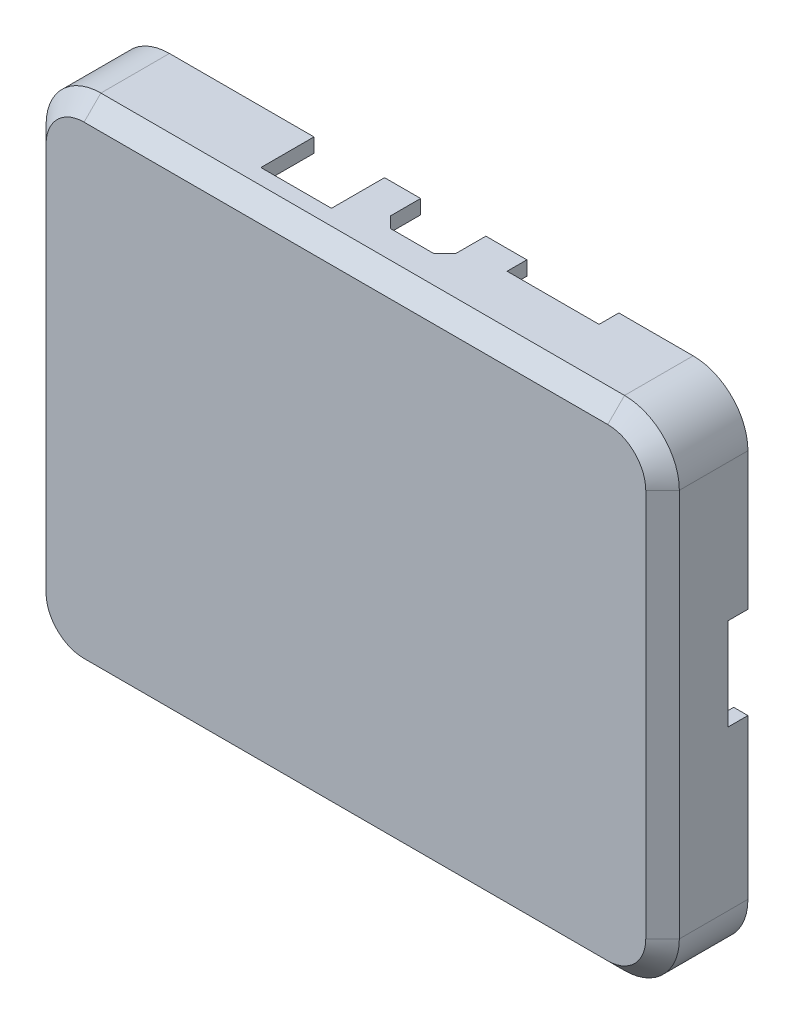
SolidWorks part; units mm, degrees
ref_plane "前基準面" through (0, 0, 0) normal (0, 0, 1) x (1, 0, 0)
ref_plane "上基準面" through (0, 0, 0) normal (0, 1, 0) x (1, 0, 0)
ref_plane "右基準面" through (0, 0, 0) normal (1, 0, 0) x (0, 0, -1)
sketch "草圖1" plane through (0, 0, 0) normal (0, 0, 1) x (1, 0, 0)
  line L1 (-44.5, 35) -> (44.5, 35)
  line L2 (-44.5, 35) -> (-44.5, -35)
  line L3 (-44.5, -35) -> (44.5, -35)
  line L4 (44.5, 35) -> (44.5, -35)
  line L5 (-44.5, 35) -> (44.5, -35) construction
  line L6 (-44.5, -35) -> (44.5, 35) construction
  point P0 (0, 0)
  dimension "D1" = 89
  dimension "D2" = 70
extrude "填料-伸長1" add sketch "草圖1" along normal blind 12
fillet "圓角1" radius 7.7 4 edges at (44.5, -35, 6) (44.5, 35, 6) (-44.5, -35, 6) (-44.5, 35, 6)
chamfer "導角1" distance 2.36 angle 45 8 edges at (-42.2447, -32.7447, 12) (-44.5, 0, 12) (-42.2447, 32.7447, 12) (0, 35, 12) (42.2447, 32.7447, 12) (44.5, 0, 12) (42.2447, -32.7447, 12) (0, -35, 12)
shell "薄殼1" thickness 2
sketch "草圖2" plane through (0, 35, 0) normal (0, 1, 0) x (1, 0, 0)
  line L0 (36.8, 0) -> (-36.8, 0) construction
  line L1 (-16.49, 0) -> (-6.57, 0)
  line L2 (-16.49, 0) -> (-16.49, -7.46)
  line L3 (-16.49, -7.46) -> (-6.57, -7.46)
  line L4 (-6.57, 0) -> (-6.57, -7.46)
  line L5 (-1.5, 0) -> (-1.5, -4.23)
  line L10 (13.43, 0) -> (26.36, 0)
  line L11 (13.43, 0) -> (13.43, -2.78)
  line L12 (13.43, -2.78) -> (26.36, -2.78)
  line L13 (26.36, 0) -> (26.36, -2.78)
  line L14 (-1.5, -4.23) -> (0.05, -5.7771)
  line L15 (0.05, -5.7771) -> (6.12, -5.7771)
  line L16 (6.12, -5.7771) -> (7.67, -4.23)
  line L17 (7.67, -4.23) -> (7.67, 0)
  line L18 (7.67, 0) -> (-1.5, 0)
  line L19 (-44.5, -9.64) -> (-44.5, 0) construction
  point P16 (3.085, -5.7771)
  point P17 (3.085, 0)
  dimension "D1" = 9.92
  dimension "D2" = 7.46
  dimension "D3" = 9.17
  dimension "D4" = 4.23
  dimension "D5" = 6.07
  dimension "D6" = 2.19
  dimension "D7" = 12.93
  dimension "D8" = 2.78
  dimension "D9" = 28.01
  dimension "D10" = 5.07
  dimension "D11" = 5.76
extrude "除料-伸長1" cut sketch "草圖2" against normal up to next
sketch "草圖3" plane through (-44.5, 0, 0) normal (-1, 0, 0) x (0, 0, 1)
  line L0 (0, 27.3) -> (0, -27.3) construction
  line L1 (0, 9.43) -> (2.78, 9.43)
  line L2 (0, 9.43) -> (0, -3.5)
  line L3 (0, -3.5) -> (2.78, -3.5)
  line L4 (2.78, 9.43) -> (2.78, -3.5)
  line L5 (9.64, -35) -> (0, -35) construction
  line L6 (0, -6.5) -> (6.7, -6.5)
  line L7 (0, -6.5) -> (0, -23.5)
  line L8 (0, -23.5) -> (6.7, -23.5)
  line L9 (6.7, -6.5) -> (6.7, -23.5)
  point P10 (1.39, -3.5)
  point P13 (4.82, -35)
  dimension "D1" = 12.93
  dimension "D2" = 2.78
  dimension "D3" = 17
  dimension "D4" = 6.7
  dimension "D5" = 3
  dimension "D6" = 11.5
extrude "除料-伸長2" cut sketch "草圖3" against normal up to next and the other way through all
sketch "草圖4" plane through (44.5, 0, 0) normal (1, 0, 0) x (0, 0, -1)
  line L0 (0, -27.3) -> (0, 27.3) construction
  line L1 (0, 8) -> (-2.78, 8)
  line L2 (0, 8) -> (0, -4.93)
  line L3 (0, -4.93) -> (-2.78, -4.93)
  line L4 (-2.78, 8) -> (-2.78, -4.93)
  line L6 (-9.64, 35) -> (0, 35) construction
  dimension "D1" = 12.93
  dimension "D2" = 2.78
  dimension "D3" = 27
extrude "除料-伸長3" cut sketch "草圖4" against normal up to next
sketch "草圖5" plane through (0, 0, 10) normal (0, 0, -1) x (-1, 0, 0)
  line L0 (-36.8, 31.8116) -> (36.8, 31.8116) construction
  line L1 (-41.3116, -27.3) -> (-41.3116, 27.3) construction
  line L2 (36.8, -31.8116) -> (-36.8, -31.8116) construction
  line L3 (41.3116, 27.3) -> (41.3116, -27.3) construction
  circle A0 centre (-35.3116, 25.8116) radius 4.5
  circle A1 centre (35.3116, 25.8116) radius 4.5
  circle A2 centre (35.3116, -25.8116) radius 4.5
  circle A3 centre (-35.3116, -25.8116) radius 4.5
  point P10 (0, 0)
  point P12 (-22.2328, 16.8849)
  point P14 (0, 0)
  point P15 (0, 0)
  point P16 (0, 0)
  point P17 (0, 0)
  point P18 (0, 0)
  point P19 (33.6885, -25.8116)
  point P20 (-33.426, -29.5018)
  point P25 (0, 0)
  dimension "D1" = 9
  dimension "D4" = 6
  dimension "D2" = 6
  dimension "D3" = 6
  dimension "D5" = 6
extrude "填料-伸長2" add sketch "草圖5" along normal up to vertex (10 mm away)
sketch "草圖6" plane through (0, 0, 0) normal (0, 0, -1) x (-1, 0, 0)
  circle A0 centre (-35.3116, 25.8116) radius 1.45
  circle A1 centre (35.3116, 25.8116) radius 1.45
  circle A2 centre (35.3116, -25.8116) radius 1.45
  circle A3 centre (-35.3116, -25.8116) radius 1.45
  dimension "D1" = 2.9
extrude "除料-伸長4" cut sketch "草圖6" against normal blind 10.9
